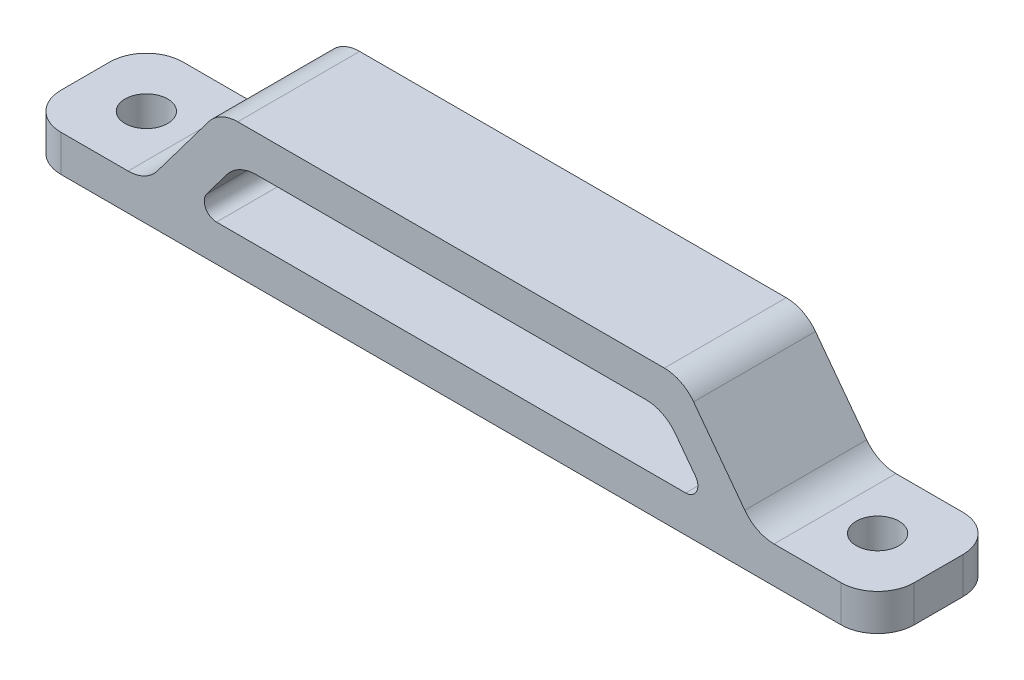
SolidWorks part; units mm, degrees
ref_plane "Front Plane" through (0, 0, 0) normal (0, 0, 1) x (1, 0, 0)
ref_plane "Top Plane" through (0, 0, 0) normal (0, 1, 0) x (1, 0, 0)
ref_plane "Right Plane" through (0, 0, 0) normal (1, 0, 0) x (0, 0, -1)
sketch "Sketch1" plane through (0, 0, 0) normal (0, 1, 0) x (1, 0, 0)
  line L0 (35, 10) -> (35, 0) construction
  line L1 (0, 0) -> (70, 0)
  line L2 (0, 0) -> (0, 10)
  line L3 (0, 10) -> (70, 10)
  line L4 (70, 0) -> (70, 10)
  circle A0 centre (5, 5) radius 1.75
  circle A2 centre (65, 5) radius 1.75
  point P11 (0, 5)
  dimension "D2" = 3.5
  dimension "D1" = 5
  dimension "D3" = 60
  dimension "D4" = 5
extrude "Boss-Extrude1" add sketch "Sketch1" along normal blind 3
sketch "Sketch2" plane through (0, 0, 0) normal (0, 0, 1) x (1, 0, 0)
  line L0 (10, 3) -> (16, 11)
  line L1 (0, 3) -> (70, 3) construction
  line L2 (16, 11) -> (54, 11)
  line L3 (35, 3) -> (35, 11) construction
  line L4 (6.75, 3) -> (3.25, 3) construction
  line L5 (60, 3) -> (54, 11)
  line L6 (10, 3) -> (60, 3)
  line L8 (5, 3) -> (5, 0) construction
  line L9 (0, 0) -> (70, 0) construction
  point P8 (35, 3)
  point P11 (0, 0)
  dimension "D1" = 8
  dimension "D2" = 5
  dimension "D3" = 6
extrude "Extrude-Thin1" add sketch "Sketch2" against normal up to surface (10 mm away) thin
sketch "Sketch3" plane through (0, 0, 0) normal (0, 0, 1) x (1, 0, 0)
  line L0 (16, 6) -> (13.75, 3)
  line L1 (13.75, 3) -> (56.25, 3)
  line L2 (56.25, 3) -> (54, 6)
  line L3 (54, 6) -> (52.5, 8) construction
  line L4 (17.5, 8) -> (16, 6) construction
  line L6 (16, 6) -> (54, 6)
  line L7 (0, 3) -> (10, 3) construction
extrude "Cut-Extrude1" cut sketch "Sketch3" against normal up to next
fillet "Fillet1" radius 3 10 edges at (16, 11, -5) (54, 11, -5) (70, 1.5, 0) (70, 1.5, -10) (0, 1.5, -10) (0, 1.5, 0) (60, 3, -5) (10, 3, -5) (52.5, 8, -5) (17.5, 8, -5)
fillet "Fillet2" radius 1 2 edges at (56.25, 3, -5) (13.75, 3, -5)
